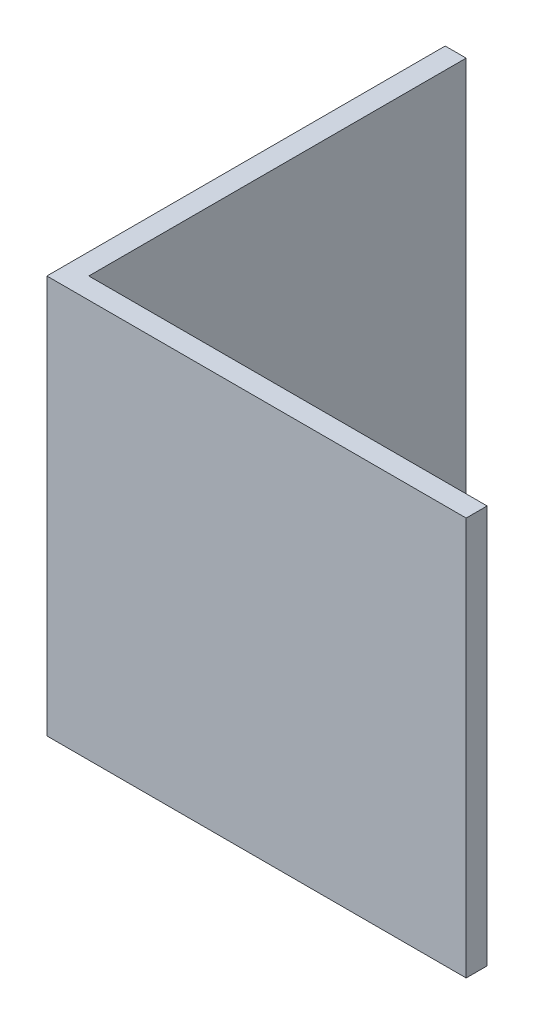
SolidWorks part; units mm, degrees
material "1060 Сплав"
ref_plane "Спереди" through (0, 0, 0) normal (0, 0, 1) x (1, 0, 0)
ref_plane "Сверху" through (0, 0, 0) normal (0, 1, 0) x (1, 0, 0)
ref_plane "Справа" through (0, 0, 0) normal (1, 0, 0) x (0, 0, -1)
sketch "Эскиз1" plane through (0, 0, 0) normal (0, 1, 0) x (1, 0, 0)
  line L0 (0, 0) -> (0, 20)
  line L1 (0, 20) -> (1, 20)
  line L2 (1, 20) -> (1, 1)
  line L3 (1, 1) -> (20, 1)
  line L4 (20, 1) -> (20, 0)
  line L5 (20, 0) -> (0, 0)
  dimension "D1" = 1
  dimension "D2" = 20
extrude "Бобышка-Вытянуть1" add sketch "Эскиз1" along normal blind 19
sketch "Sketch1" plane through (0, 0, -20) normal (0, 0, -1) x (-1, 0, 0)
  line L4 (-1, 0) -> (0, 0)
  line L5 (0, 0) -> (0, 19)
  line L6 (0, 19) -> (-1, 19)
  line L7 (-1, 19) -> (-1, 0)
  line L8 (-1, 0) -> (0, 0)
  line L9 (0, 0) -> (0, 19)
  line L10 (0, 19) -> (-1, 19)
  line L11 (-1, 19) -> (-1, 0)
  dimension "D1" = 0
extrude "Cut-Extrude1" cut sketch "Sketch1" against normal blind 1
